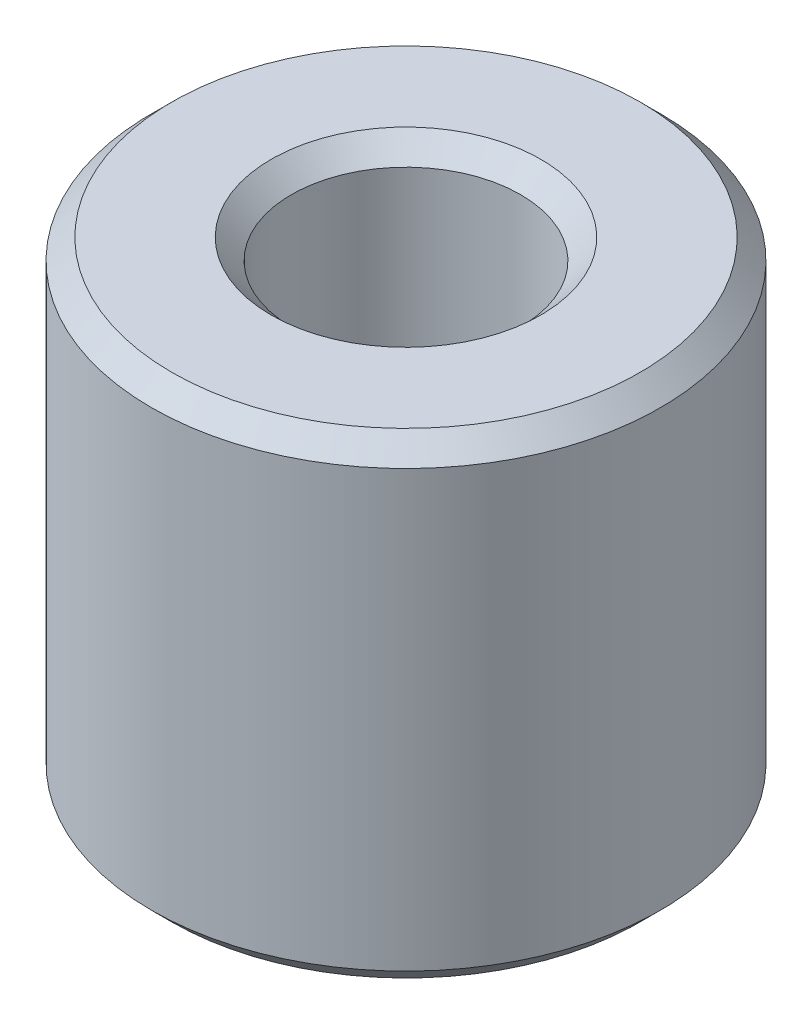
SolidWorks part; units mm, degrees
material "PET-G"
ref_plane "Front Plane" through (0, 0, 0) normal (0, 0, 1) x (1, 0, 0)
ref_plane "Top Plane" through (0, 0, 0) normal (0, 1, 0) x (1, 0, 0)
ref_plane "Right Plane" through (0, 0, 0) normal (1, 0, 0) x (0, 0, -1)
sketch "Sketch1" plane through (0, 0, 0) normal (0, 1, 0) x (1, 0, 0)
  circle A0 centre (0, 0) radius 4.5
  circle A1 centre (0, 0) radius 10
  dimension "D1" = 9
  dimension "D2" = 20
extrude "Body" add sketch "Sketch1" along normal blind 18.7
chamfer "Chamfer 0.8" distance 0.8 angle 45 4 edges at (0, 0, 4.5) (0, 0, 10) (0, 18.7, 10) (0, 18.7, 4.5)
